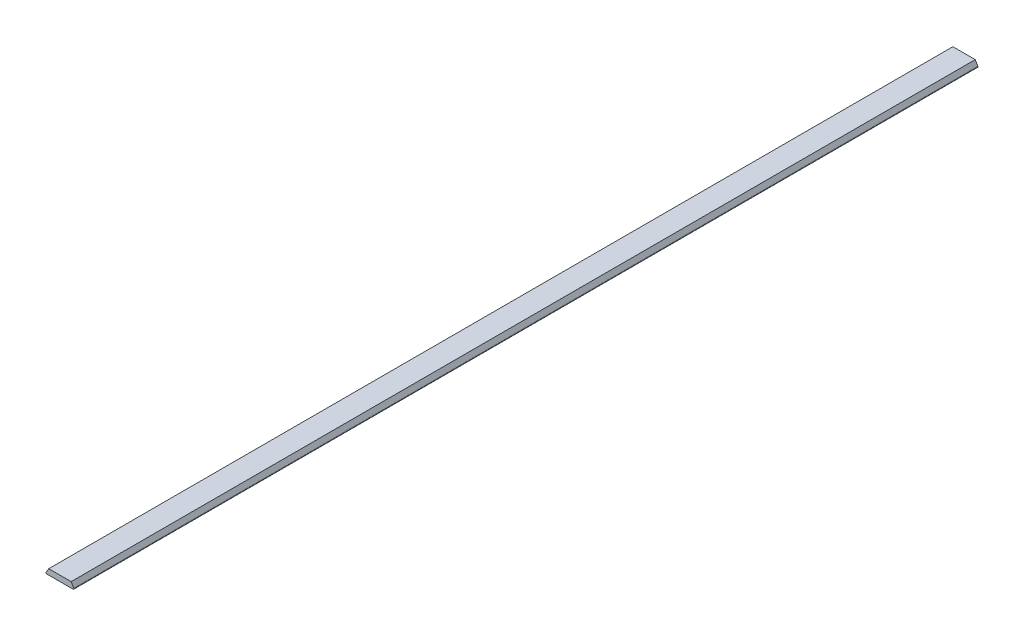
SolidWorks part; units mm, degrees
ref_plane "Front Plane" through (0, 0, 0) normal (0, 0, 1) x (1, 0, 0)
ref_plane "Top Plane" through (0, 0, 0) normal (0, 1, 0) x (1, 0, 0)
ref_plane "Right Plane" through (0, 0, 0) normal (1, 0, 0) x (0, 0, -1)
sketch "Sketch1" plane through (0, 0, 0) normal (0, 0, 1) x (1, 0, 0)
  line L1 (0, 5.5) -> (-2.5968, 1.1334)
  line L2 (-1.9522, 0) -> (0, 0)
  line L4 (0, 5.5) -> (22, 5.5)
  line L6 (22, 0) -> (0, 0)
  line L7 (11, 11.1244) -> (11, -4.8444) construction
  line L8 (23.9522, 0) -> (22, 0)
  line L9 (22, 5.5) -> (24.5968, 1.1334)
  arc A0 (-1.9522, 0) -> (-2.5968, 1.1334) centre (-1.9522, 0.75) cw
  arc A1 (23.9522, 0) -> (24.5968, 1.1334) centre (23.9522, 0.75) ccw
  point P12 (11, 5.5)
  dimension "D2" = 0.75
  dimension "D1" = 5.5
  dimension "D5" = 22
  dimension "D3" = 59.26
extrude "Boss-Extrude1" add sketch "Sketch1" along normal blind 889
equation "\"WedgeHeight\"= 5.5mm'with tolerance"
equation "\"WedgeFillet\"= 0.75mm"
equation "\"WedgeExtend\"= 3mm"
equation "\"SlotWidth\"= 22mm"
equation "\"D1@Sketch1\"= \"WedgeHeight\""
equation "\"D2@Sketch1\"= \"WedgeFillet\""
equation "\"D5@Sketch1\"= \"SlotWidth\""
equation "\"AxialLength\"= 925mm"
equation "\"StepHeight\"= 18mm"
equation "\"D1@Boss-Extrude1\"= \"AxialLength\" - \"StepHeight\" * 2"
equation "\"WedgeAngle\"= 59.2563169deg"
equation "\"D3@Sketch1\"= \"WedgeAngle\""
